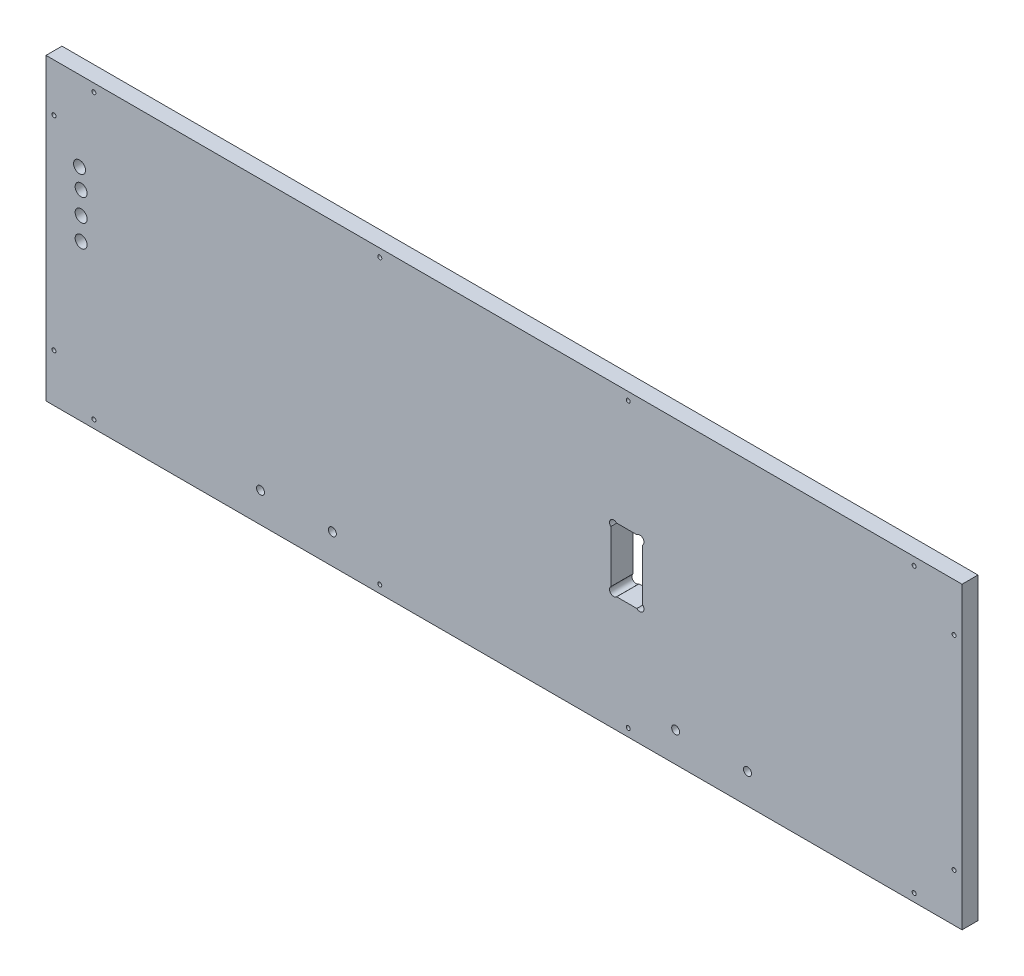
SolidWorks part; units mm, degrees
material "Pine"
ref_plane "Front Plane" through (0, 0, 0) normal (0, 0, 1) x (1, 0, 0)
ref_plane "Top Plane" through (0, 0, 0) normal (0, 1, 0) x (1, 0, 0)
ref_plane "Right Plane" through (0, 0, 0) normal (1, 0, 0) x (0, 0, -1)
sketch "Sketch1" plane through (0, 0, 0) normal (0, 0, 1) x (1, 0, 0)
  line L0 (-5300.6625, 1520.825) -> (-5451.475, 1520.825)
  line L1 (-5456.2375, 1384.3) -> (-5456.2375, 1516.0625)
  line L2 (-5557.8375, 1546.225) -> (-5194.3, 1546.225)
  line L3 (-5557.8375, 1539.875) -> (-5194.3, 1539.875)
  line L4 (-5297.4875, 1377.95) -> (-5454.65, 1377.95)
  line L5 (-5291.1375, 1384.3) -> (-5291.1375, 1516.0625)
  line L6 (-5300.6625, 1525.5875) -> (-5451.475, 1525.5875)
  line L7 (-5461, 1384.3) -> (-5461, 1516.0625)
  line L8 (-5297.4875, 1382.7125) -> (-5454.65, 1382.7125)
  line L9 (-5295.9, 1384.3) -> (-5295.9, 1516.0625)
  line L10 (-5740.4, 998.5375) -> (-5740.4, 1181.1)
  line L11 (-5740.4, 1181.1) -> (-5512.5938, 1181.1)
  line L12 (-5512.5938, 1181.1) -> (-5512.5938, 998.5375)
  line L13 (-5512.5938, 998.5375) -> (-5740.4, 998.5375)
  line L14 (-5258.5938, 1181.1) -> (-5486.4, 1181.1)
  line L15 (-5258.5938, 998.5375) -> (-5258.5938, 1181.1)
  line L16 (-5486.4, 998.5375) -> (-5258.5938, 998.5375)
  line L17 (-5486.4, 1181.1) -> (-5486.4, 998.5375)
  line L18 (-5740.4, 898.525) -> (-5011.7375, 898.525)
  line L19 (-5168.1062, 1384.3) -> (-5168.1062, 1392.2375)
  line L20 (-5176.0437, 1400.175) -> (-5245.8937, 1400.175)
  line L21 (-5253.8313, 1392.2375) -> (-5253.8313, 1384.3)
  line L22 (-5451.475, 1512.8875) -> (-5451.475, 1384.3)
  line L23 (-5303.8375, 1516.0625) -> (-5448.3, 1516.0625)
  line L24 (-5498.3062, 1384.3) -> (-5451.475, 1384.3)
  line L25 (-5253.8313, 1384.3) -> (-5300.6625, 1384.3)
  line L26 (-5584.0312, 1384.3) -> (-5740.4, 1384.3)
  line L27 (-5564.1875, 1536.7) -> (-5740.4, 1536.7)
  line L28 (-5740.4, 1357.3125) -> (-5740.4, 1206.5)
  line L29 (-5011.7375, 1357.3125) -> (-5740.4, 1357.3125)
  line L30 (-5011.7375, 1206.5) -> (-5011.7375, 1357.3125)
  line L31 (-5740.4, 1206.5) -> (-5011.7375, 1206.5)
  line L32 (-4765.675, 1549.4) -> (-4978.4, 1549.4)
  line L33 (-4765.675, 1397) -> (-4765.675, 1549.4)
  line L34 (-4978.4, 1397) -> (-4765.675, 1397)
  line L35 (-4978.4, 1549.4) -> (-4978.4, 1397)
  line L36 (-4765.675, 1371.6) -> (-4978.4, 1371.6)
  line L37 (-4765.675, 1219.2) -> (-4765.675, 1371.6)
  line L38 (-4978.4, 1219.2) -> (-4765.675, 1219.2)
  line L39 (-4978.4, 1371.6) -> (-4978.4, 1219.2)
  line L40 (-5284.7875, 803.275) -> (-5272.0875, 803.275)
  line L41 (-5187.95, 1536.7) -> (-5011.7375, 1536.7)
  line L42 (-5300.6625, 1384.3) -> (-5300.6625, 1512.8875)
  line L43 (-5740.4, 1536.7) -> (-5740.4, 1384.3)
  line L44 (-5557.8375, 1536.7) -> (-5557.8375, 1549.4)
  line L45 (-5557.8375, 1549.4) -> (-5194.3, 1549.4)
  line L46 (-5194.3, 1549.4) -> (-5194.3, 1536.7)
  line L47 (-5011.7375, 1536.7) -> (-5011.7375, 1384.3)
  line L48 (-5011.7375, 1384.3) -> (-5168.1062, 1384.3)
  line L49 (-5498.3062, 1384.3) -> (-5498.3062, 1392.2375)
  line L50 (-5506.2437, 1400.175) -> (-5576.0938, 1400.175)
  line L51 (-5584.0312, 1392.2375) -> (-5584.0312, 1384.3)
  line L52 (-5740.4, 660.4) -> (-5740.4, 898.525)
  line L53 (-5011.7375, 898.525) -> (-5011.7375, 660.4)
  line L54 (-5011.7375, 660.4) -> (-5740.4, 660.4)
  line L55 (-5291.1375, 803.275) -> (-5291.1375, 752.475)
  line L56 (-5265.7375, 752.475) -> (-5265.7375, 803.275)
  line L57 (-5284.7875, 752.475) -> (-5272.0875, 752.475)
  arc A0 (-5451.475, 1520.825) -> (-5456.2375, 1516.0625) centre (-5451.475, 1516.0625) ccw
  arc A1 (-5461, 1384.3) -> (-5454.65, 1377.95) centre (-5454.65, 1384.3) ccw
  arc A2 (-5297.4875, 1377.95) -> (-5291.1375, 1384.3) centre (-5297.4875, 1384.3) ccw
  circle A3 centre (-5037.9312, 1233.4875) radius 1.5875
  circle A4 centre (-5037.9312, 1328.7375) radius 1.5875
  circle A5 centre (-5714.2063, 1233.4875) radius 1.5875
  circle A6 centre (-5714.2063, 1328.7375) radius 1.5875
  circle A7 centre (-5018.0875, 1333.5) radius 1.5875
  circle A8 centre (-5018.0875, 1231.9) radius 1.5875
  circle A9 centre (-5734.05, 1231.9) radius 1.5875
  circle A10 centre (-5734.05, 1333.5) radius 1.5875
  circle A11 centre (-5734.05, 1511.3) radius 1.5875
  circle A12 centre (-5734.05, 1409.7) radius 1.5875
  circle A13 centre (-5018.0875, 1511.3) radius 1.5875
  circle A14 centre (-5018.0875, 1409.7) radius 1.5875
  arc A15 (-5557.8375, 1546.225) -> (-5557.8375, 1539.875) centre (-5557.8375, 1543.05) ccw
  arc A16 (-5194.3, 1539.875) -> (-5194.3, 1546.225) centre (-5194.3, 1543.05) ccw
  arc A17 (-5291.1375, 1516.0625) -> (-5300.6625, 1525.5875) centre (-5300.6625, 1516.0625) ccw
  arc A18 (-5451.475, 1525.5875) -> (-5461, 1516.0625) centre (-5451.475, 1516.0625) ccw
  arc A19 (-5456.2375, 1384.3) -> (-5454.65, 1382.7125) centre (-5454.65, 1384.3) ccw
  arc A20 (-5297.4875, 1382.7125) -> (-5295.9, 1384.3) centre (-5297.4875, 1384.3) ccw
  arc A21 (-5295.9, 1516.0625) -> (-5300.6625, 1520.825) centre (-5300.6625, 1516.0625) ccw
  circle A22 centre (-5702.3, 892.175) radius 1.5875
  circle A23 centre (-5734.05, 860.425) radius 1.5875
  circle A24 centre (-5474.8906, 892.175) radius 1.5875
  circle A25 centre (-5277.2469, 892.175) radius 1.5875
  circle A26 centre (-5049.8375, 892.175) radius 1.5875
  circle A27 centre (-5018.0875, 860.425) radius 1.5875
  circle A28 centre (-5296.6938, 1174.75) radius 1.5875
  circle A29 centre (-5448.3, 1174.75) radius 1.5875
  circle A30 centre (-5264.9437, 1155.7) radius 1.5875
  circle A31 centre (-5264.9437, 1023.9375) radius 1.5875
  circle A32 centre (-5518.9438, 1155.7) radius 1.5875
  circle A33 centre (-5518.9438, 1023.9375) radius 1.5875
  circle A34 centre (-5702.3, 1004.8875) radius 1.5875
  circle A35 centre (-5550.6937, 1004.8875) radius 1.5875
  arc A36 (-5576.0938, 1400.175) -> (-5584.0312, 1392.2375) centre (-5576.0938, 1392.2375) ccw
  arc A37 (-5168.1062, 1392.2375) -> (-5176.0437, 1400.175) centre (-5176.0437, 1392.2375) ccw
  arc A38 (-5245.8937, 1400.175) -> (-5253.8313, 1392.2375) centre (-5245.8937, 1392.2375) ccw
  arc A39 (-5448.3, 1516.0625) -> (-5451.475, 1512.8875) centre (-5448.3, 1512.8875) ccw
  arc A40 (-5284.7875, 803.275) -> (-5291.1375, 803.275) centre (-5287.9625, 803.275) ccw
  circle A41 centre (-5679.2812, 1026.3187) radius 1.5875
  circle A42 centre (-5679.2812, 1153.3187) radius 1.5875
  circle A43 centre (-5571.3313, 1153.3187) radius 1.5875
  circle A44 centre (-5571.3313, 1026.3187) radius 1.5875
  circle A45 centre (-5317.3312, 1153.3187) radius 1.5875
  circle A46 centre (-5317.3312, 1026.3187) radius 1.5875
  circle A47 centre (-5425.2812, 1026.3187) radius 1.5875
  circle A48 centre (-5425.2812, 1153.3187) radius 1.5875
  arc A49 (-5194.3, 1536.7) -> (-5187.95, 1536.7) centre (-5191.125, 1536.7) ccw
  arc A50 (-5564.1875, 1536.7) -> (-5557.8375, 1536.7) centre (-5561.0125, 1536.7) ccw
  arc A51 (-5300.6625, 1512.8875) -> (-5303.8375, 1516.0625) centre (-5303.8375, 1512.8875) ccw
  arc A52 (-5498.3062, 1392.2375) -> (-5506.2437, 1400.175) centre (-5506.2437, 1392.2375) ccw
  circle A53 centre (-5712.46, 784.225) radius 4.7625
  arc A54 (-5272.0875, 752.475) -> (-5265.7375, 752.475) centre (-5268.9125, 752.475) ccw
  arc A55 (-5291.1375, 752.475) -> (-5284.7875, 752.475) centre (-5287.9625, 752.475) ccw
  circle A56 centre (-5182.3938, 684.2125) radius 3.175
  circle A57 centre (-5239.5437, 684.2125) radius 3.175
  circle A58 centre (-5512.5938, 684.2125) radius 3.175
  circle A59 centre (-5569.7437, 684.2125) radius 3.175
  circle A60 centre (-5474.8906, 666.75) radius 1.5875
  circle A61 centre (-5277.2469, 666.75) radius 1.5875
  circle A62 centre (-5734.05, 698.5) radius 1.5875
  circle A63 centre (-5702.3, 666.75) radius 1.5875
  circle A64 centre (-5049.8375, 666.75) radius 1.5875
  circle A65 centre (-5018.0875, 698.5) radius 1.5875
  circle A66 centre (-5713.73, 835.025) radius 4.7625
  circle A67 centre (-5712.46, 819.785) radius 4.7625
  circle A68 centre (-5712.46, 802.005) radius 4.7625
  circle A69 centre (-5714.2063, 1314.45) radius 3.175
  circle A70 centre (-5037.9312, 1314.45) radius 3.175
  arc A71 (-5265.7375, 803.275) -> (-5272.0875, 803.275) centre (-5268.9125, 803.275) ccw
  ellipse E0 centre (-5371.3062, 1089.8188) end of major axis (-5277.6438, 1089.8188) minor radius 65.0875
  ellipse E1 centre (-5625.3062, 1089.8188) end of major axis (-5531.6438, 1089.8188) minor radius 65.0875
sketch "Sketch2" plane through (0, 0, 0) normal (0, 0, 1) x (1, 0, 0)
  line L0 (-5011.7375, 660.4) -> (-5011.7375, 898.525)
  line L1 (-5011.7375, 898.525) -> (-5740.4, 898.525)
  line L2 (-5740.4, 898.525) -> (-5740.4, 660.4)
  line L3 (-5740.4, 660.4) -> (-5011.7375, 660.4)
extrude "Extrude1" add sketch "Sketch2" against normal blind 17.78
sketch "Sketch3" plane through (0, 0, 0) normal (0, 0, 1) x (1, 0, 0)
  line L0 (-5291.1375, 803.275) -> (-5291.1375, 752.475)
  line L1 (-5265.7375, 803.275) -> (-5265.7375, 752.475)
  line L2 (-5291.1375, 803.275) -> (-5265.7375, 803.275)
  line L3 (-5291.1375, 752.475) -> (-5265.7375, 752.475)
  circle A0 centre (-5702.3, 892.175) radius 1.5875
  circle A1 centre (-5734.05, 860.425) radius 1.5875
  circle A6 centre (-5734.05, 698.5) radius 1.5875
  circle A7 centre (-5702.3, 666.75) radius 1.5875
  circle A8 centre (-5569.7437, 684.2125) radius 3.175
  circle A9 centre (-5512.5938, 684.2125) radius 3.175
  circle A10 centre (-5474.8906, 666.75) radius 1.5875
  circle A11 centre (-5277.2469, 666.75) radius 1.5875
  circle A12 centre (-5239.5437, 684.2125) radius 3.175
  circle A13 centre (-5182.3938, 684.2125) radius 3.175
  circle A14 centre (-5049.8375, 666.75) radius 1.5875
  circle A15 centre (-5018.0875, 698.5) radius 1.5875
  circle A16 centre (-5018.0875, 860.425) radius 1.5875
  circle A17 centre (-5049.8375, 892.175) radius 1.5875
  circle A18 centre (-5277.2469, 892.175) radius 1.5875
  circle A19 centre (-5474.8906, 892.175) radius 1.5875
extrude "Cut-Extrude1" cut sketch "Sketch3" against normal up to surface (17.78 mm away) up to face at (-5376.0688, 779.4625, -17.78)
sketch "Sketch6" plane through (0, 0, 0) normal (0, 0, 1) x (1, 0, 0)
  line L0 (-5291.1375, 803.275) -> (-5288.8026, 800.9401) construction
  line L1 (-5265.7375, 803.275) -> (-5268.0724, 800.9401) construction
  line L2 (-5291.1375, 752.475) -> (-5288.8026, 754.8099) construction
  line L3 (-5265.7375, 752.475) -> (-5268.0724, 754.8099) construction
  circle A0 centre (-5288.8026, 800.9401) radius 3.302
  circle A1 centre (-5268.0724, 800.9401) radius 3.302
  circle A2 centre (-5288.8026, 754.8099) radius 3.302
  circle A3 centre (-5268.0724, 754.8099) radius 3.302
extrude "Cut-Extrude4" cut sketch "Sketch6" against normal up to surface (17.78 mm away) up to face at (-5278.4375, 777.875, -17.78)
sketch "Sketch4" plane through (0, 660.4, 0) normal (0, -1, 0) x (1, 0, 0)
  line L0 (-5291.1375, -17.78) -> (-5291.1375, -9.525)
  line L1 (-5740.4, -17.78) -> (-5011.7375, -17.78) construction
  line L2 (-5291.1375, -149.5425) -> (-5291.1375, -17.78) construction
  line L3 (-5291.1375, -9.525) -> (-5461, -9.525)
  line L4 (-5461, -9.525) -> (-5461, -17.78)
  line L5 (-5461, -17.78) -> (-5461, -149.5425) construction
  line L6 (-5461, -17.78) -> (-5291.1375, -17.78)
extrude "Cut-Extrude2" cut sketch "Sketch4" against normal blind 3.175
sketch "Sketch5" plane through (0, 0, -17.78) normal (0, 0, -1) x (-1, 0, 0)
  line L0 (5011.7375, 660.4) -> (5113.3375, 660.4)
  line L1 (5291.1375, 660.4) -> (5011.7375, 660.4) construction
  line L2 (5113.3375, 660.4) -> (5113.3375, 673.1)
  line L3 (5113.3375, 673.1) -> (5024.4375, 673.1)
  line L4 (5024.4375, 673.1) -> (5024.4375, 885.825)
  line L5 (5024.4375, 885.825) -> (5727.7, 885.825)
  line L6 (5727.7, 885.825) -> (5727.7, 673.1)
  line L7 (5727.7, 673.1) -> (5638.8, 673.1)
  line L8 (5638.8, 673.1) -> (5638.8, 660.4)
  line L9 (5740.4, 660.4) -> (5461, 660.4) construction
  line L10 (5638.8, 660.4) -> (5740.4, 660.4)
  line L11 (5740.4, 660.4) -> (5740.4, 898.525)
  line L12 (5740.4, 898.525) -> (5011.7375, 898.525)
  line L13 (5011.7375, 898.525) -> (5011.7375, 660.4)
  dimension "D1" = 101.6
  dimension "D2" = 12.7
  dimension "D3" = 12.7
  dimension "D4" = 12.7
  dimension "D5" = 12.7
  dimension "D6" = 101.6
  dimension "D7" = 12.7
extrude "Cut-Extrude3" cut sketch "Sketch5" against normal blind 5.08
sketch "Sketch7" plane through (0, 0, -17.78) normal (0, 0, -1) x (-1, 0, 0)
  line L0 (5113.3375, 673.1) -> (5110.6125, 671.2352) construction
  line L1 (5638.8, 673.1) -> (5641.525, 671.2352) construction
  circle A0 centre (5641.525, 671.2352) radius 3.302
  circle A1 centre (5110.6125, 671.2352) radius 3.302
extrude "Cut-Extrude5" cut sketch "Sketch7" against normal up to surface (5.08 mm away) up to face at (-5735.6375, 860.425, -12.7)
sketch "Sketch8" plane through (0, 0, -17.78) normal (0, 0, -1) x (-1, 0, 0)
  line L0 (5727.7, 885.825) -> (5727.7, 673.1) construction
  circle A0 centre (5713.73, 835.025) radius 4.7625
  circle A1 centre (5712.46, 819.785) radius 4.7625
  circle A2 centre (5712.46, 802.005) radius 4.7625
  circle A3 centre (5712.46, 784.225) radius 4.7625
  dimension "D2" = 15.24
  dimension "D1" = 15.24
  dimension "D3" = 15.24
  dimension "D4" = 13.97
extrude "Cut-Extrude6" cut sketch "Sketch8" against normal up to surface (17.78 mm away) up to face at (-5278.4375, 777.875, 0)
